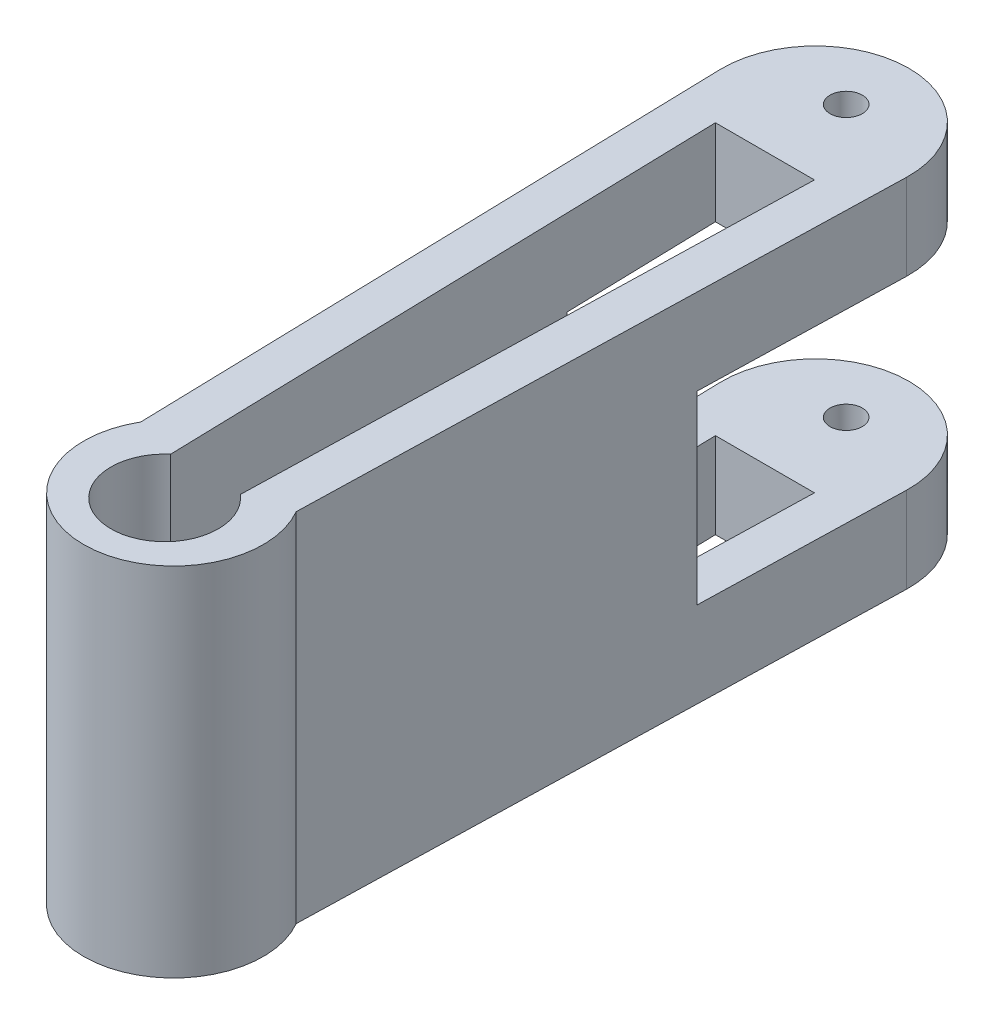
SolidWorks part; units mm, degrees
ref_plane "Front Plane" through (0, 0, 0) normal (0, 0, 1) x (1, 0, 0)
ref_plane "Top Plane" through (0, 0, 0) normal (0, 1, 0) x (1, 0, 0)
ref_plane "Right Plane" through (0, 0, 0) normal (1, 0, 0) x (0, 0, -1)
sketch "Sketch1" plane through (0, 0, 0) normal (0, 1, 0) x (1, 0, 0)
  line L0 (-13.9448, -0.3652) -> (-11.6169, -89.2652)
  line L1 (13.9448, -0.3652) -> (11.6169, -89.2652)
  line L2 (0, 15.9405) -> (0, -57.1464) construction
  arc A0 (13.9448, -0.3652) -> (-13.9448, -0.3652) centre (0, 0) ccw
  arc A1 (-11.6169, -89.2652) -> (11.6169, -89.2652) centre (0, -95.9895) ccw
  dimension "D2" = 1.5
  dimension "D3" = 1.5
  dimension "D4" = 88.9
  dimension "D5" = 88.9
extrude "Boss-Extrude1" add sketch "Sketch1" along normal blind 53.34 contours L0 A1 L1 A0
ref_plane "Plane1" through (0, 0, 0.3652) normal (0, 0, -1) x (-1, 0, 0)
sketch "Sketch2" plane through (0, 0, 0.3652) normal (0, 0, -1) x (-1, 0, 0)
  line L1 (-13.8535, 41.783) -> (16.0684, 41.783)
  line L2 (-13.8535, 41.783) -> (-13.8535, 37.211)
  line L3 (-13.8535, 37.211) -> (16.0684, 37.211)
  line L4 (16.0684, 41.783) -> (16.0684, 37.211)
  line L5 (13.4226, 53.34) -> (-13.4226, 53.34) construction
  dimension "D1" = 4.572
  dimension "D2" = 11.557
sketch "Sketch3" plane through (0, 0, 0) normal (0, -1, 0) x (1, 0, 0)
  line L0 (-5.2137, 91.2104) -> (-7.404, 7.5684)
  line L1 (7.404, 7.5684) -> (5.2137, 91.2104)
  line L2 (13.9448, 0.3652) -> (11.6169, 89.2652)
  line L3 (-11.6169, 89.2652) -> (-13.9448, 0.3652)
  line L4 (13.9448, 0.3652) -> (11.6169, 89.2652)
  line L5 (-11.6169, 89.2652) -> (-13.9448, 0.3652)
  line L6 (7.404, 7.5684) -> (-11.1568, 7.5684)
  line L7 (7.597, 0.1989) -> (5.2137, 91.2104) construction
  line L8 (-5.2137, 91.2104) -> (-7.597, 0.1989) construction
  arc A2 (-13.9448, 0.3652) -> (13.9448, 0.3652) centre (0, 0) ccw
  arc A3 (11.6169, 89.2652) -> (-11.6169, 89.2652) centre (0, 95.9895) ccw
  arc A4 (-13.9448, 0.3652) -> (13.9448, 0.3652) centre (0, 0) ccw
  arc A5 (11.6169, 89.2652) -> (-11.6169, 89.2652) centre (0, 95.9895) ccw
  arc A7 (5.2137, 91.2104) -> (-5.2137, 91.2104) centre (0, 95.9895) ccw construction
  arc A8 (5.2137, 91.2104) -> (-5.2137, 91.2104) centre (0, 97.3127) ccw
  arc A10 (-7.597, 0.1989) -> (7.597, 0.1989) centre (0, 0) ccw construction
  dimension "D1" = 0
  dimension "D2" = 6.35
sketch "Sketch4" plane through (13.9448, 0, 0.3652) normal (0.9997, 0, 0.0262) x (0.0262, 0, -0.9997)
  line L0 (0, 53.34) -> (0, 0) construction
  line L1 (-30.5363, 12.827) -> (30.5363, 12.827)
  line L2 (-30.5363, 12.827) -> (-30.5363, 40.513)
  line L3 (-30.5363, 40.513) -> (30.5363, 40.513)
  line L4 (30.5363, 12.827) -> (30.5363, 40.513)
  line L5 (-30.5363, 12.827) -> (30.5363, 40.513) construction
  line L6 (-30.5363, 40.513) -> (30.5363, 12.827) construction
  point P0 (0, 26.67)
  dimension "D1" = 27.686
extrude "Cut-Extrude3" cut sketch "Sketch4" against normal through all
sketch "Sketch5" plane through (0, 53.34, 0) normal (0, 1, 0) x (1, 0, 0)
  line L0 (7.404, -7.5684) -> (5.2137, -91.2104) construction
  line L1 (-5.2137, -91.2104) -> (-7.404, -7.5684) construction
  line L2 (-13.9448, -0.3652) -> (-11.6169, -89.2652)
  line L3 (11.6169, -89.2652) -> (13.9448, -0.3652)
  line L4 (-13.9448, -0.3652) -> (-11.6169, -89.2652)
  line L5 (11.6169, -89.2652) -> (13.9448, -0.3652)
  line L6 (7.404, -7.5684) -> (-11.1568, -7.5684) construction
  line L7 (7.404, -7.5684) -> (5.2137, -91.2104)
  line L8 (-5.2137, -91.2104) -> (-7.404, -7.5684)
  line L9 (7.404, -7.5684) -> (-7.404, -7.5684)
  arc A0 (-5.2137, -91.2104) -> (5.2137, -91.2104) centre (0, -97.3127) ccw construction
  arc A1 (-5.2137, -91.2104) -> (5.2137, -91.2104) centre (0, -97.3127) ccw
  arc A2 (13.9448, -0.3652) -> (-13.9448, -0.3652) centre (0, 0) ccw
  arc A3 (-11.6169, -89.2652) -> (11.6169, -89.2652) centre (0, -95.9895) ccw
  arc A4 (13.9448, -0.3652) -> (-13.9448, -0.3652) centre (0, 0) ccw
  arc A5 (-11.6169, -89.2652) -> (11.6169, -89.2652) centre (0, -95.9895) ccw
  dimension "D1" = 0
extrude "Cut-Extrude5" cut sketch "Sketch5" against normal through all flip side to cut
sketch "Sketch6" plane through (0, 53.34, 0) normal (0, 1, 0) x (1, 0, 0)
  circle A0 centre (0, 4.5787) radius 2.413
  dimension "D1" = 4.826
extrude "Cut-Extrude6" cut sketch "Sketch6" against normal through all
